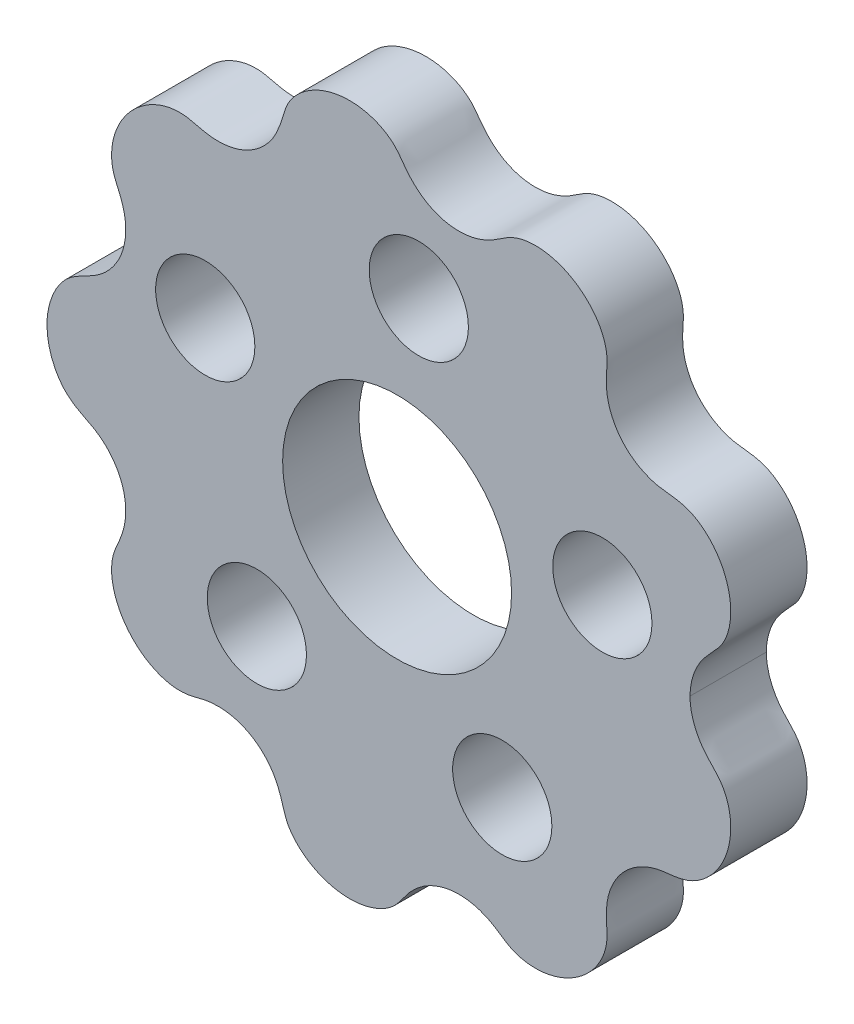
SolidWorks part; units mm, degrees
ref_plane "前视基准面" through (0, 0, 0) normal (0, 0, 1) x (1, 0, 0)
ref_plane "上视基准面" through (0, 0, 0) normal (0, 1, 0) x (1, 0, 0)
ref_plane "右视基准面" through (0, 0, 0) normal (1, 0, 0) x (0, 0, -1)
sketch "草图1" plane through (0, 0, 0) normal (0, 0, 1) x (1, 0, 0)
  line L1 (20.5154, 0) -> (-27.3443, 0) construction
  circle A0 centre (0, 0) radius 6
  spline S0 degree 4 poles (15.4078, 8.5516) (15.5295, 8.4988) (15.7665, 8.3783) (16.0954, 8.1616) (16.4836, 7.8143) (16.8177, 7.4226) (17.0967, 6.997) (17.3205, 6.5428) (17.4876, 6.0676) (17.5964, 5.5785) (17.6455, 5.0823) (17.6342, 4.6444) (17.5834, 4.2711) (17.5188, 3.9944) (17.464, 3.8115) (17.4096, 3.6599) (17.3652, 3.5484) (17.3015, 3.4107) (17.264, 3.3361) (17.1959, 3.2126) (17.1357, 3.1153) (17.0539, 2.995) (16.9466, 2.855) (16.8227, 2.7161) (16.6845, 2.5745) (16.5593, 2.4464) (16.4489, 2.3292) (16.3152, 2.1788) (16.1636, 1.9906) (15.9279, 1.6517) (15.6648, 1.128) (15.5052, 0.5273) (15.4814, -0.1226) (15.5605, -0.6649) (15.6861, -1.0955) (15.8612, -1.486) (16.0723, -1.8343) (16.3083, -2.1405) (16.555, -2.4111) (16.8315, -2.6803) (17.0942, -2.9918) (17.3183, -3.376) (17.4934, -3.8233) (17.6004, -4.2921) (17.6447, -4.77) (17.6284, -5.3454) (17.5114, -6.0091) (17.2782, -6.6442) (16.9371, -7.2268) (16.5751, -7.677) (16.2309, -8.0126) (15.8447, -8.2997) (15.4203, -8.5266) (15.0412, -8.6571) (14.7274, -8.7164) (14.4754, -8.7433) (14.2878, -8.7614) (14.0538, -8.7875) (13.7745, -8.8319) (13.4356, -8.9131) (13.0465, -9.0545) (12.6619, -9.2527) (12.2934, -9.5127) (11.8848, -9.8966) (11.5541, -10.3501) (11.3139, -10.8552) (11.1745, -11.3721) (11.1177, -11.7725) (11.1056, -12.1567) (11.1235, -12.5208) (11.1616, -12.9028) (11.1565, -13.3076) (11.077, -13.7432) (10.9196, -14.1964) (10.6973, -14.6217) (10.4213, -15.0134) (10.0386, -15.4384) (9.5199, -15.8691) (8.9276, -16.2044) (8.283, -16.4293) (7.7098, -16.5364) (7.234, -16.5664) (6.7578, -16.5334) (6.2917, -16.4312) (5.9188, -16.2837) (5.6393, -16.1218) (5.4292, -15.9788) (5.2755, -15.8737) (5.0812, -15.7457) (4.8406, -15.6034) (4.5282, -15.45) (4.1358, -15.3101) (3.7069, -15.2171) (3.2474, -15.184) (2.6836, -15.2243) (2.1404, -15.368) (1.6382, -15.6067) (1.2083, -15.9148) (0.9137, -16.185) (0.6623, -16.4706) (0.4458, -16.7597) (0.2309, -17.073) (-0.0332, -17.3739) (-0.3682, -17.6486) (-0.768, -17.8866) (-1.1977, -18.0655) (-1.6462, -18.1881) (-2.2006, -18.2717) (-2.8603, -18.2759) (-3.5137, -18.1653) (-4.1373, -17.9436) (-4.6414, -17.6775) (-5.0344, -17.4059) (-5.3889, -17.0847) (-5.6928, -16.7155) (-5.9179, -16.3359) (-6.0638, -15.9596) (-6.159, -15.5889) (-6.2647, -15.2412) (-6.4052, -14.8846) (-6.5924, -14.5278) (-6.8329, -14.1799) (-7.1315, -13.853) (-7.5621, -13.4948) (-8.0571, -13.22) (-8.5978, -13.0422) (-9.1415, -12.9705) (-9.5543, -12.969) (-9.8973, -13.0066) (-10.1698, -13.0579) (-10.3944, -13.1114) (-10.5734, -13.1573) (-10.8176, -13.2192) (-11.1325, -13.2755) (-11.5352, -13.2877) (-12.0154, -13.2238) (-12.4807, -13.0889) (-12.9231, -12.8929) (-13.4234, -12.5936) (-13.9487, -12.1614) (-14.3889, -11.6423) (-14.7282, -11.0568) (-14.9397, -10.5253) (-15.0609, -10.069) (-15.1224, -9.6002) (-15.1158, -9.1277) (-15.0429, -8.6926) (-14.9083, -8.3067) (-14.7402, -7.9578) (-14.5979, -7.619) (-14.4775, -7.2504) (-14.3944, -6.8508) (-14.3504, -6.3116) (-14.4076, -5.7493) (-14.5695, -5.2059) (-14.8297, -4.7031) (-15.0937, -4.3326) (-15.3919, -4.0176) (-15.7112, -3.7566) (-16.0007, -3.5689) (-16.2445, -3.4365) (-16.493, -3.3133) (-16.7635, -3.1884) (-17.0822, -3.0075) (-17.4253, -2.7249) (-17.7404, -2.3697) (-18.0007, -1.9724) (-18.2069, -1.5452) (-18.3936, -0.9986) (-18.4981, -0.4259) (-18.5152, 0.1061) (-18.4674, 0.5843) (-18.3989, 0.9586) (-18.2998, 1.3264) (-18.162, 1.6833) (-17.9848, 2.0237) (-17.8279, 2.2658) (-17.712, 2.4219) (-17.6193, 2.534) (-17.5563, 2.6054) (-17.4986, 2.6666) (-17.4495, 2.7166) (-17.3994, 2.7656) (-17.3573, 2.8048) (-17.2912, 2.8633) (-17.2206, 2.9222) (-17.136, 2.9878) (-17.0307, 3.0623) (-16.9018, 3.1436) (-16.7502, 3.2263) (-16.5557, 3.3218) (-16.3265, 3.43) (-16.0686, 3.5654) (-15.7905, 3.7403) (-15.5336, 3.9357) (-15.2572, 4.1901) (-15.0215, 4.4653) (-14.827, 4.7542) (-14.6447, 5.1032) (-14.5035, 5.4638) (-14.396, 5.904) (-14.3548, 6.4206) (-14.386, 6.8105) (-14.4341, 7.0695) (-14.4644, 7.1976) knots 0 0 0 0 0 0.006514 0.013028 0.019259 0.02549 0.031721 0.037951 0.044056 0.05016 0.056265 0.062369 0.065499 0.06863 0.070195 0.07176 0.073325 0.074891 0.076327 0.077763 0.079199 0.080635 0.083508 0.08638 0.088356 0.090332 0.092308 0.094284 0.098235 0.102187 0.112552 0.122904 0.128397 0.133889 0.139373 0.144856 0.149346 0.153836 0.158325 0.162815 0.168293 0.173771 0.180047 0.186323 0.191803 0.197283 0.208243 0.219261 0.22477 0.230279 0.236542 0.242804 0.248311 0.253817 0.25613 0.258442 0.260755 0.263067 0.267692 0.272317 0.277832 0.283347 0.288867 0.294387 0.305265 0.310695 0.316125 0.320597 0.325069 0.329541 0.334013 0.33944 0.344867 0.351176 0.357485 0.362911 0.368338 0.37919 0.390445 0.396072 0.401699 0.407747 0.413796 0.419421 0.425045 0.42733 0.429615 0.431901 0.434186 0.438756 0.443326 0.448958 0.454591 0.46023 0.46587 0.476611 0.481972 0.487332 0.491763 0.496194 0.500625 0.505056 0.510412 0.515769 0.521798 0.527828 0.533186 0.538544 0.549261 0.560079 0.565488 0.570897 0.577186 0.583476 0.588886 0.594295 0.598754 0.603212 0.60767 0.612128 0.61754 0.622952 0.628374 0.633796 0.644955 0.650528 0.656101 0.660637 0.665172 0.667439 0.669707 0.671974 0.674242 0.679808 0.685374 0.691655 0.697935 0.703504 0.709072 0.720208 0.731179 0.736664 0.74215 0.748228 0.754305 0.759791 0.765276 0.769783 0.774291 0.778798 0.783306 0.788793 0.794281 0.805279 0.810848 0.816417 0.821979 0.82754 0.832078 0.836617 0.838886 0.841155 0.845694 0.85125 0.856805 0.862867 0.868928 0.874485 0.880041 0.891155 0.897379 0.900491 0.903603 0.909827 0.916051 0.919226 0.9224 0.923987 0.925574 0.926368 0.927162 0.927955 0.928749 0.929811 0.930873 0.931936 0.932998 0.935122 0.937247 0.939371 0.941496 0.945745 0.9497 0.953655 0.957611 0.961566 0.968116 0.971391 0.974665 0.980874 0.987083 0.993541 1 1 1 1 1 construction
  spline S1 degree 4 poles (15.5, 0) (15.5006, -0.1109) (15.5122, -0.3337) (15.5608, -0.6658) (15.6861, -1.0955) (15.8612, -1.486) (16.0723, -1.8343) (16.3083, -2.1405) (16.555, -2.4111) (16.8315, -2.6803) (17.0942, -2.9918) (17.3183, -3.376) (17.4934, -3.8233) (17.6004, -4.2921) (17.6447, -4.77) (17.6284, -5.3454) (17.5114, -6.0091) (17.2782, -6.6442) (16.9371, -7.2268) (16.5751, -7.677) (16.2309, -8.0126) (15.8447, -8.2997) (15.4203, -8.5266) (15.0412, -8.6571) (14.7274, -8.7164) (14.4754, -8.7433) (14.2878, -8.7614) (14.0538, -8.7875) (13.7745, -8.8319) (13.4356, -8.9131) (13.0465, -9.0545) (12.6619, -9.2527) (12.2934, -9.5127) (11.8848, -9.8966) (11.5541, -10.3501) (11.3139, -10.8552) (11.1745, -11.3721) (11.1177, -11.7725) (11.1056, -12.1567) (11.1235, -12.5208) (11.1616, -12.9028) (11.1565, -13.3076) (11.077, -13.7432) (10.9196, -14.1964) (10.6973, -14.6217) (10.4213, -15.0134) (10.0386, -15.4384) (9.5199, -15.8691) (8.9276, -16.2044) (8.283, -16.4293) (7.7098, -16.5364) (7.234, -16.5664) (6.7578, -16.5334) (6.2917, -16.4312) (5.9188, -16.2837) (5.6393, -16.1218) (5.4292, -15.9788) (5.2755, -15.8737) (5.0812, -15.7457) (4.8406, -15.6034) (4.5282, -15.45) (4.1358, -15.3101) (3.7069, -15.2171) (3.2474, -15.184) (2.6836, -15.2243) (2.1404, -15.368) (1.6382, -15.6067) (1.2083, -15.9148) (0.9137, -16.185) (0.6623, -16.4706) (0.4458, -16.7597) (0.2309, -17.073) (-0.0332, -17.3739) (-0.3682, -17.6486) (-0.768, -17.8866) (-1.1977, -18.0655) (-1.6462, -18.1881) (-2.2006, -18.2717) (-2.8603, -18.2759) (-3.5137, -18.1653) (-4.1373, -17.9436) (-4.6414, -17.6775) (-5.0344, -17.4059) (-5.3889, -17.0847) (-5.6928, -16.7155) (-5.9179, -16.3359) (-6.0638, -15.9596) (-6.159, -15.5889) (-6.2647, -15.2412) (-6.4052, -14.8846) (-6.5924, -14.5278) (-6.8329, -14.1799) (-7.1315, -13.853) (-7.5621, -13.4948) (-8.0571, -13.22) (-8.5978, -13.0422) (-9.1415, -12.9705) (-9.5543, -12.969) (-9.8973, -13.0066) (-10.1698, -13.0579) (-10.3944, -13.1114) (-10.5734, -13.1573) (-10.8176, -13.2192) (-11.1325, -13.2755) (-11.5352, -13.2877) (-12.0154, -13.2238) (-12.4807, -13.0889) (-12.9231, -12.8929) (-13.4234, -12.5936) (-13.9487, -12.1614) (-14.3889, -11.6423) (-14.7282, -11.0568) (-14.9397, -10.5253) (-15.0609, -10.069) (-15.1224, -9.6002) (-15.1158, -9.1277) (-15.0429, -8.6926) (-14.9083, -8.3067) (-14.7402, -7.9578) (-14.5979, -7.619) (-14.4775, -7.2504) (-14.3944, -6.8508) (-14.3504, -6.3116) (-14.4076, -5.7493) (-14.5695, -5.2059) (-14.8297, -4.7031) (-15.0937, -4.3326) (-15.3919, -4.0176) (-15.7112, -3.7566) (-16.0007, -3.5689) (-16.2445, -3.4365) (-16.493, -3.3133) (-16.7635, -3.1884) (-17.0822, -3.0075) (-17.4253, -2.7249) (-17.7404, -2.3697) (-18.0007, -1.9724) (-18.2069, -1.5452) (-18.3924, -1.0021) (-18.4739, -0.5585) (-18.499, -0.2227) (-18.5, 0) knots 0.12295 0.12295 0.12295 0.12295 0.12295 0.128397 0.133889 0.139373 0.144856 0.149346 0.153836 0.158325 0.162815 0.168293 0.173771 0.180047 0.186323 0.191803 0.197283 0.208243 0.219261 0.22477 0.230279 0.236542 0.242804 0.248311 0.253817 0.25613 0.258442 0.260755 0.263067 0.267692 0.272317 0.277832 0.283347 0.288867 0.294387 0.305265 0.310695 0.316125 0.320597 0.325069 0.329541 0.334013 0.33944 0.344867 0.351176 0.357485 0.362911 0.368338 0.37919 0.390445 0.396072 0.401699 0.407747 0.413796 0.419421 0.425045 0.42733 0.429615 0.431901 0.434186 0.438756 0.443326 0.448958 0.454591 0.46023 0.46587 0.476611 0.481972 0.487332 0.491763 0.496194 0.500625 0.505056 0.510412 0.515769 0.521798 0.527828 0.533186 0.538544 0.549261 0.560079 0.565488 0.570897 0.577186 0.583476 0.588886 0.594295 0.598754 0.603212 0.60767 0.612128 0.61754 0.622952 0.628374 0.633796 0.644955 0.650528 0.656101 0.660637 0.665172 0.667439 0.669707 0.671974 0.674242 0.679808 0.685374 0.691655 0.697935 0.703504 0.709072 0.720208 0.731179 0.736664 0.74215 0.748228 0.754305 0.759791 0.765276 0.769783 0.774291 0.778798 0.783306 0.788793 0.794281 0.805279 0.810848 0.816417 0.821979 0.82754 0.832078 0.836617 0.838886 0.841155 0.845694 0.85125 0.856805 0.862867 0.868928 0.874485 0.880041 0.890975 0.890975 0.890975 0.890975 0.890975
  spline S2 degree 4 poles (15.5, 0) (15.5006, 0.1109) (15.5122, 0.3337) (15.5608, 0.6658) (15.6861, 1.0955) (15.8612, 1.486) (16.0723, 1.8343) (16.3083, 2.1405) (16.555, 2.4111) (16.8315, 2.6803) (17.0942, 2.9918) (17.3183, 3.376) (17.4934, 3.8233) (17.6004, 4.2921) (17.6447, 4.77) (17.6284, 5.3454) (17.5114, 6.0091) (17.2782, 6.6442) (16.9371, 7.2268) (16.5751, 7.677) (16.2309, 8.0126) (15.8447, 8.2997) (15.4203, 8.5266) (15.0412, 8.6571) (14.7274, 8.7164) (14.4754, 8.7433) (14.2878, 8.7614) (14.0538, 8.7875) (13.7745, 8.8319) (13.4356, 8.9131) (13.0465, 9.0545) (12.6619, 9.2527) (12.2934, 9.5127) (11.8848, 9.8966) (11.5541, 10.3501) (11.3139, 10.8552) (11.1745, 11.3721) (11.1177, 11.7725) (11.1056, 12.1567) (11.1235, 12.5208) (11.1616, 12.9028) (11.1565, 13.3076) (11.077, 13.7432) (10.9196, 14.1964) (10.6973, 14.6217) (10.4213, 15.0134) (10.0386, 15.4384) (9.5199, 15.8691) (8.9276, 16.2044) (8.283, 16.4293) (7.7098, 16.5364) (7.234, 16.5664) (6.7578, 16.5334) (6.2917, 16.4312) (5.9188, 16.2837) (5.6393, 16.1218) (5.4292, 15.9788) (5.2755, 15.8737) (5.0812, 15.7457) (4.8406, 15.6034) (4.5282, 15.45) (4.1358, 15.3101) (3.7069, 15.2171) (3.2474, 15.184) (2.6836, 15.2243) (2.1404, 15.368) (1.6382, 15.6067) (1.2083, 15.9148) (0.9137, 16.185) (0.6623, 16.4706) (0.4458, 16.7597) (0.2309, 17.073) (-0.0332, 17.3739) (-0.3682, 17.6486) (-0.768, 17.8866) (-1.1977, 18.0655) (-1.6462, 18.1881) (-2.2006, 18.2717) (-2.8603, 18.2759) (-3.5137, 18.1653) (-4.1373, 17.9436) (-4.6414, 17.6775) (-5.0344, 17.4059) (-5.3889, 17.0847) (-5.6928, 16.7155) (-5.9179, 16.3359) (-6.0638, 15.9596) (-6.159, 15.5889) (-6.2647, 15.2412) (-6.4052, 14.8846) (-6.5924, 14.5278) (-6.8329, 14.1799) (-7.1315, 13.853) (-7.5621, 13.4948) (-8.0571, 13.22) (-8.5978, 13.0422) (-9.1415, 12.9705) (-9.5543, 12.969) (-9.8973, 13.0066) (-10.1698, 13.0579) (-10.3944, 13.1114) (-10.5734, 13.1573) (-10.8176, 13.2192) (-11.1325, 13.2755) (-11.5352, 13.2877) (-12.0154, 13.2238) (-12.4807, 13.0889) (-12.9231, 12.8929) (-13.4234, 12.5936) (-13.9487, 12.1614) (-14.3889, 11.6423) (-14.7282, 11.0568) (-14.9397, 10.5253) (-15.0609, 10.069) (-15.1224, 9.6002) (-15.1158, 9.1277) (-15.0429, 8.6926) (-14.9083, 8.3067) (-14.7402, 7.9578) (-14.5979, 7.619) (-14.4775, 7.2504) (-14.3944, 6.8508) (-14.3504, 6.3116) (-14.4076, 5.7493) (-14.5695, 5.2059) (-14.8297, 4.7031) (-15.0937, 4.3326) (-15.3919, 4.0176) (-15.7112, 3.7566) (-16.0007, 3.5689) (-16.2445, 3.4365) (-16.493, 3.3133) (-16.7635, 3.1884) (-17.0822, 3.0075) (-17.4253, 2.7249) (-17.7404, 2.3697) (-18.0007, 1.9724) (-18.2069, 1.5452) (-18.3924, 1.0021) (-18.4739, 0.5585) (-18.499, 0.2227) (-18.5, 0) knots 0.12295 0.12295 0.12295 0.12295 0.12295 0.128397 0.133889 0.139373 0.144856 0.149346 0.153836 0.158325 0.162815 0.168293 0.173771 0.180047 0.186323 0.191803 0.197283 0.208243 0.219261 0.22477 0.230279 0.236542 0.242804 0.248311 0.253817 0.25613 0.258442 0.260755 0.263067 0.267692 0.272317 0.277832 0.283347 0.288867 0.294387 0.305265 0.310695 0.316125 0.320597 0.325069 0.329541 0.334013 0.33944 0.344867 0.351176 0.357485 0.362911 0.368338 0.37919 0.390445 0.396072 0.401699 0.407747 0.413796 0.419421 0.425045 0.42733 0.429615 0.431901 0.434186 0.438756 0.443326 0.448958 0.454591 0.46023 0.46587 0.476611 0.481972 0.487332 0.491763 0.496194 0.500625 0.505056 0.510412 0.515769 0.521798 0.527828 0.533186 0.538544 0.549261 0.560079 0.565488 0.570897 0.577186 0.583476 0.588886 0.594295 0.598754 0.603212 0.60767 0.612128 0.61754 0.622952 0.628374 0.633796 0.644955 0.650528 0.656101 0.660637 0.665172 0.667439 0.669707 0.671974 0.674242 0.679808 0.685374 0.691655 0.697935 0.703504 0.709072 0.720208 0.731179 0.736664 0.74215 0.748228 0.754305 0.759791 0.765276 0.769783 0.774291 0.778798 0.783306 0.788793 0.794281 0.805279 0.810848 0.816417 0.821979 0.82754 0.832078 0.836617 0.838886 0.841155 0.845694 0.85125 0.856805 0.862867 0.868928 0.874485 0.880041 0.890975 0.890975 0.890975 0.890975 0.890975
extrude "凸台-拉伸1" add sketch "草图1" along normal blind 4
sketch "草图2" plane through (0, 0, 4) normal (0, 0, 1) x (1, 0, 0)
  circle A1 centre (5.5114, -9.5197) radius 2.6
  circle A9 centre (-7.3506, -8.1834) radius 2.6
  circle A10 centre (-10.0544, 4.462) radius 2.6
  circle A11 centre (1.1367, 10.9411) radius 2.6
  circle A12 centre (10.7569, 2.2999) radius 2.6
  point P13 (0, 0)
  point P22 (0, 0)
  dimension "D1" = 5
extrude "切除-拉伸1" cut sketch "草图2" against normal blind 4
sketch "草图3" plane through (0, 0, 4) normal (0, 0, 1) x (1, 0, 0)
  spline S0 degree 4 poles (1623.4562, 1732.6571) (562.2442, -2347.7402) (172.4823, 104.3908) (-26.5264, 22.8102) (-18.2069, -1.5452) (-18.0007, -1.9724) (-17.7404, -2.3697) (-17.4253, -2.7249) (-17.0822, -3.0075) (-16.7635, -3.1884) (-16.493, -3.3133) (-16.2445, -3.4365) (-16.0007, -3.5689) (-15.7112, -3.7566) (-15.3919, -4.0176) (-15.0937, -4.3326) (-14.8297, -4.7031) (-14.5695, -5.2059) (-14.4076, -5.7493) (-14.3504, -6.3116) (-14.3944, -6.8508) (-14.4775, -7.2504) (-14.5979, -7.619) (-14.7402, -7.9578) (-14.9083, -8.3067) (-15.0429, -8.6926) (-15.1158, -9.1277) (-15.1224, -9.6002) (-15.0609, -10.069) (-14.9397, -10.5253) (-14.7282, -11.0568) (-14.3889, -11.6423) (-13.9487, -12.1614) (-13.4234, -12.5936) (-12.9231, -12.8929) (-12.4807, -13.0889) (-12.0154, -13.2238) (-11.5352, -13.2877) (-11.1325, -13.2755) (-10.8176, -13.2192) (-10.5734, -13.1573) (-10.3944, -13.1114) (-10.1698, -13.0579) (-9.8973, -13.0066) (-9.5543, -12.969) (-9.1415, -12.9705) (-8.5978, -13.0422) (-8.0571, -13.22) (-7.5621, -13.4948) (-7.1315, -13.853) (-6.8329, -14.1799) (-6.5924, -14.5278) (-6.4052, -14.8846) (-6.2647, -15.2412) (-6.159, -15.5889) (-6.0638, -15.9596) (-5.9179, -16.3359) (-5.6928, -16.7155) (-5.3889, -17.0847) (-5.0344, -17.4059) (-4.6414, -17.6775) (-4.1373, -17.9436) (-3.5137, -18.1653) (-2.8603, -18.2759) (-2.2006, -18.2717) (-1.6462, -18.1881) (-1.1977, -18.0655) (-0.768, -17.8866) (-0.3682, -17.6486) (-0.0332, -17.3739) (0.2309, -17.073) (0.4458, -16.7597) (0.6623, -16.4706) (0.9137, -16.185) (1.2083, -15.9148) (1.6382, -15.6067) (2.1404, -15.368) (2.6836, -15.2243) (3.2474, -15.184) (3.7069, -15.2171) (4.1358, -15.3101) (4.5282, -15.45) (4.8406, -15.6034) (5.0812, -15.7457) (5.2755, -15.8737) (5.4292, -15.9788) (5.6393, -16.1218) (5.9188, -16.2837) (6.2917, -16.4312) (6.7578, -16.5334) (7.234, -16.5664) (7.7098, -16.5364) (8.283, -16.4293) (8.9276, -16.2044) (9.5199, -15.8691) (10.0386, -15.4384) (10.4213, -15.0134) (10.6973, -14.6217) (10.9196, -14.1964) (11.077, -13.7432) (11.1565, -13.3076) (11.1616, -12.9028) (11.1235, -12.5208) (11.1056, -12.1567) (11.1177, -11.7725) (11.1745, -11.3721) (11.3139, -10.8552) (11.5541, -10.3501) (11.8848, -9.8966) (12.2934, -9.5127) (12.6619, -9.2527) (13.0465, -9.0545) (13.4356, -8.9131) (13.7745, -8.8319) (14.0538, -8.7875) (14.2878, -8.7614) (14.4754, -8.7433) (14.7274, -8.7164) (15.0412, -8.6571) (15.4203, -8.5266) (15.8447, -8.2997) (16.2309, -8.0126) (16.5751, -7.677) (16.9371, -7.2268) (17.2782, -6.6442) (17.5114, -6.0091) (17.6284, -5.3454) (17.6447, -4.77) (17.6004, -4.2921) (17.4934, -3.8233) (17.3183, -3.376) (17.0942, -2.9918) (16.8315, -2.6803) (16.555, -2.4111) (16.3083, -2.1405) (16.0723, -1.8343) (15.8612, -1.486) (15.6861, -1.0955) (13.1065, 7.7509) (43.9529, 23.7285) (146.1118, -134.5096) (-2647.3681, -1370.9416) knots -1.109563 -1.109563 -1.109563 -1.109563 -1.109563 0.133883 0.139439 0.144996 0.151057 0.157119 0.162675 0.16823 0.172769 0.175038 0.177307 0.181846 0.186384 0.191946 0.197507 0.203076 0.208646 0.219643 0.225131 0.230618 0.235126 0.239633 0.244141 0.248648 0.254134 0.259619 0.265697 0.271774 0.27726 0.282745 0.293717 0.304853 0.310421 0.315989 0.32227 0.32855 0.334116 0.339682 0.34195 0.344217 0.346485 0.348753 0.353288 0.357823 0.363396 0.368969 0.380129 0.385551 0.390973 0.396384 0.401796 0.406254 0.410712 0.415171 0.419629 0.425038 0.430448 0.436738 0.443027 0.448436 0.453845 0.464663 0.47538 0.480738 0.486096 0.492126 0.498156 0.503512 0.508869 0.513299 0.51773 0.522161 0.526592 0.531952 0.537313 0.548055 0.553694 0.559334 0.564966 0.570598 0.575168 0.579739 0.582024 0.584309 0.586594 0.588879 0.594504 0.600128 0.606177 0.612225 0.617852 0.62348 0.634734 0.645587 0.651013 0.656439 0.662748 0.669057 0.674484 0.679912 0.684383 0.688855 0.693327 0.697799 0.703229 0.708659 0.719537 0.725057 0.730577 0.736092 0.741607 0.746232 0.750857 0.753169 0.755482 0.757794 0.760107 0.765614 0.77112 0.777383 0.783645 0.789154 0.794663 0.805681 0.816641 0.822121 0.827601 0.833877 0.840153 0.845631 0.85111 0.855599 0.860089 0.864578 0.869068 0.874551 0.880035 0.885528 1.319982 1.319982 1.319982 1.319982 1.319982 only from (-18.5, 0) to (15.5, 0) construction
  spline S1 degree 4 poles (-18.5, 0) (-18.499, -0.2227) (-18.4739, -0.5585) (-18.3924, -1.0021) (-18.2069, -1.5452) (-18.0007, -1.9724) (-17.7404, -2.3697) (-17.4253, -2.7249) (-17.0822, -3.0075) (-16.7635, -3.1884) (-16.493, -3.3133) (-16.2445, -3.4365) (-16.0007, -3.5689) (-15.7112, -3.7566) (-15.3919, -4.0176) (-15.0937, -4.3326) (-14.8297, -4.7031) (-14.5695, -5.2059) (-14.4076, -5.7493) (-14.3504, -6.3116) (-14.3944, -6.8508) (-14.4775, -7.2504) (-14.5979, -7.619) (-14.7402, -7.9578) (-14.9083, -8.3067) (-15.0429, -8.6926) (-15.1158, -9.1277) (-15.1224, -9.6002) (-15.0609, -10.069) (-14.9397, -10.5253) (-14.7282, -11.0568) (-14.3889, -11.6423) (-13.9487, -12.1614) (-13.4234, -12.5936) (-12.9231, -12.8929) (-12.4807, -13.0889) (-12.0154, -13.2238) (-11.5352, -13.2877) (-11.1325, -13.2755) (-10.8176, -13.2192) (-10.5734, -13.1573) (-10.3944, -13.1114) (-10.1698, -13.0579) (-9.8973, -13.0066) (-9.5543, -12.969) (-9.1415, -12.9705) (-8.5978, -13.0422) (-8.0571, -13.22) (-7.5621, -13.4948) (-7.1315, -13.853) (-6.8329, -14.1799) (-6.5924, -14.5278) (-6.4052, -14.8846) (-6.2647, -15.2412) (-6.159, -15.5889) (-6.0638, -15.9596) (-5.9179, -16.3359) (-5.6928, -16.7155) (-5.3889, -17.0847) (-5.0344, -17.4059) (-4.6414, -17.6775) (-4.1373, -17.9436) (-3.5137, -18.1653) (-2.8603, -18.2759) (-2.2006, -18.2717) (-1.6462, -18.1881) (-1.1977, -18.0655) (-0.768, -17.8866) (-0.3682, -17.6486) (-0.0332, -17.3739) (0.2309, -17.073) (0.4458, -16.7597) (0.6623, -16.4706) (0.9137, -16.185) (1.2083, -15.9148) (1.6382, -15.6067) (2.1404, -15.368) (2.6836, -15.2243) (3.2474, -15.184) (3.7069, -15.2171) (4.1358, -15.3101) (4.5282, -15.45) (4.8406, -15.6034) (5.0812, -15.7457) (5.2755, -15.8737) (5.4292, -15.9788) (5.6393, -16.1218) (5.9188, -16.2837) (6.2917, -16.4312) (6.7578, -16.5334) (7.234, -16.5664) (7.7098, -16.5364) (8.283, -16.4293) (8.9276, -16.2044) (9.5199, -15.8691) (10.0386, -15.4384) (10.4213, -15.0134) (10.6973, -14.6217) (10.9196, -14.1964) (11.077, -13.7432) (11.1565, -13.3076) (11.1616, -12.9028) (11.1235, -12.5208) (11.1056, -12.1567) (11.1177, -11.7725) (11.1745, -11.3721) (11.3139, -10.8552) (11.5541, -10.3501) (11.8848, -9.8966) (12.2934, -9.5127) (12.6619, -9.2527) (13.0465, -9.0545) (13.4356, -8.9131) (13.7745, -8.8319) (14.0538, -8.7875) (14.2878, -8.7614) (14.4754, -8.7433) (14.7274, -8.7164) (15.0412, -8.6571) (15.4203, -8.5266) (15.8447, -8.2997) (16.2309, -8.0126) (16.5751, -7.677) (16.9371, -7.2268) (17.2782, -6.6442) (17.5114, -6.0091) (17.6284, -5.3454) (17.6447, -4.77) (17.6004, -4.2921) (17.4934, -3.8233) (17.3183, -3.376) (17.0942, -2.9918) (16.8315, -2.6803) (16.555, -2.4111) (16.3083, -2.1405) (16.0723, -1.8343) (15.8612, -1.486) (15.6861, -1.0955) (15.5608, -0.6658) (15.5122, -0.3337) (15.5006, -0.1109) (15.5, 0) knots 0.12295 0.12295 0.12295 0.12295 0.12295 0.133883 0.139439 0.144996 0.151057 0.157119 0.162675 0.16823 0.172769 0.175038 0.177307 0.181846 0.186384 0.191946 0.197507 0.203076 0.208646 0.219643 0.225131 0.230618 0.235126 0.239633 0.244141 0.248648 0.254134 0.259619 0.265697 0.271774 0.27726 0.282745 0.293717 0.304853 0.310421 0.315989 0.32227 0.32855 0.334116 0.339682 0.34195 0.344217 0.346485 0.348753 0.353288 0.357823 0.363396 0.368969 0.380129 0.385551 0.390973 0.396384 0.401796 0.406254 0.410712 0.415171 0.419629 0.425038 0.430448 0.436738 0.443027 0.448436 0.453845 0.464663 0.47538 0.480738 0.486096 0.492126 0.498156 0.503512 0.508869 0.513299 0.51773 0.522161 0.526592 0.531952 0.537313 0.548055 0.553694 0.559334 0.564966 0.570598 0.575168 0.579739 0.582024 0.584309 0.586594 0.588879 0.594504 0.600128 0.606177 0.612225 0.617852 0.62348 0.634734 0.645587 0.651013 0.656439 0.662748 0.669057 0.674484 0.679912 0.684383 0.688855 0.693327 0.697799 0.703229 0.708659 0.719537 0.725057 0.730577 0.736092 0.741607 0.746232 0.750857 0.753169 0.755482 0.757794 0.760107 0.765614 0.77112 0.777383 0.783645 0.789154 0.794663 0.805681 0.816641 0.822121 0.827601 0.833877 0.840153 0.845631 0.85111 0.855599 0.860089 0.864578 0.869068 0.874551 0.880035 0.885528 0.890975 0.890975 0.890975 0.890975 0.890975
  spline S2 degree 4 poles (-2647.7561, 1371.1133) (146.1223, 134.5259) (43.955, -23.7296) (13.1064, -7.7512) (15.6861, 1.0955) (15.8612, 1.486) (16.0723, 1.8343) (16.3083, 2.1405) (16.555, 2.4111) (16.8315, 2.6803) (17.0942, 2.9918) (17.3183, 3.376) (17.4934, 3.8233) (17.6004, 4.2921) (17.6447, 4.77) (17.6284, 5.3454) (17.5114, 6.0091) (17.2782, 6.6442) (16.9371, 7.2268) (16.5751, 7.677) (16.2309, 8.0126) (15.8447, 8.2997) (15.4203, 8.5266) (15.0412, 8.6571) (14.7274, 8.7164) (14.4754, 8.7433) (14.2878, 8.7614) (14.0538, 8.7875) (13.7745, 8.8319) (13.4356, 8.9131) (13.0465, 9.0545) (12.6619, 9.2527) (12.2934, 9.5127) (11.8848, 9.8966) (11.5541, 10.3501) (11.3139, 10.8552) (11.1745, 11.3721) (11.1177, 11.7725) (11.1056, 12.1567) (11.1235, 12.5208) (11.1616, 12.9028) (11.1565, 13.3076) (11.077, 13.7432) (10.9196, 14.1964) (10.6973, 14.6217) (10.4213, 15.0134) (10.0386, 15.4384) (9.5199, 15.8691) (8.9276, 16.2044) (8.283, 16.4293) (7.7098, 16.5364) (7.234, 16.5664) (6.7578, 16.5334) (6.2917, 16.4312) (5.9188, 16.2837) (5.6393, 16.1218) (5.4292, 15.9788) (5.2755, 15.8737) (5.0812, 15.7457) (4.8406, 15.6034) (4.5282, 15.45) (4.1358, 15.3101) (3.7069, 15.2171) (3.2474, 15.184) (2.6836, 15.2243) (2.1404, 15.368) (1.6382, 15.6067) (1.2083, 15.9148) (0.9137, 16.185) (0.6623, 16.4706) (0.4458, 16.7597) (0.2309, 17.073) (-0.0332, 17.3739) (-0.3682, 17.6486) (-0.768, 17.8866) (-1.1977, 18.0655) (-1.6462, 18.1881) (-2.2006, 18.2717) (-2.8603, 18.2759) (-3.5137, 18.1653) (-4.1373, 17.9436) (-4.6414, 17.6775) (-5.0344, 17.4059) (-5.3889, 17.0847) (-5.6928, 16.7155) (-5.9179, 16.3359) (-6.0638, 15.9596) (-6.159, 15.5889) (-6.2647, 15.2412) (-6.4052, 14.8846) (-6.5924, 14.5278) (-6.8329, 14.1799) (-7.1315, 13.853) (-7.5621, 13.4948) (-8.0571, 13.22) (-8.5978, 13.0422) (-9.1415, 12.9705) (-9.5543, 12.969) (-9.8973, 13.0066) (-10.1698, 13.0579) (-10.3944, 13.1114) (-10.5734, 13.1573) (-10.8176, 13.2192) (-11.1325, 13.2755) (-11.5352, 13.2877) (-12.0154, 13.2238) (-12.4807, 13.0889) (-12.9231, 12.8929) (-13.4234, 12.5936) (-13.9487, 12.1614) (-14.3889, 11.6423) (-14.7282, 11.0568) (-14.9397, 10.5253) (-15.0609, 10.069) (-15.1224, 9.6002) (-15.1158, 9.1277) (-15.0429, 8.6926) (-14.9083, 8.3067) (-14.7402, 7.9578) (-14.5979, 7.619) (-14.4775, 7.2504) (-14.3944, 6.8508) (-14.3504, 6.3116) (-14.4076, 5.7493) (-14.5695, 5.2059) (-14.8297, 4.7031) (-15.0937, 4.3326) (-15.3919, 4.0176) (-15.7112, 3.7566) (-16.0007, 3.5689) (-16.2445, 3.4365) (-16.493, 3.3133) (-16.7635, 3.1884) (-17.0822, 3.0075) (-17.4253, 2.7249) (-17.7404, 2.3697) (-18.0007, 1.9724) (-18.2069, 1.5452) (-26.5265, -22.8105) (172.4881, -104.3932) (562.2612, 2347.8471) (1623.5182, -1732.8954) knots -0.306073 -0.306073 -0.306073 -0.306073 -0.306073 0.128397 0.133889 0.139373 0.144856 0.149346 0.153836 0.158325 0.162815 0.168293 0.173771 0.180047 0.186323 0.191803 0.197283 0.208243 0.219261 0.22477 0.230279 0.236542 0.242804 0.248311 0.253817 0.25613 0.258442 0.260755 0.263067 0.267692 0.272317 0.277832 0.283347 0.288867 0.294387 0.305265 0.310695 0.316125 0.320597 0.325069 0.329541 0.334013 0.33944 0.344867 0.351176 0.357485 0.362911 0.368338 0.37919 0.390445 0.396072 0.401699 0.407747 0.413796 0.419421 0.425045 0.42733 0.429615 0.431901 0.434186 0.438756 0.443326 0.448958 0.454591 0.46023 0.46587 0.476611 0.481972 0.487332 0.491763 0.496194 0.500625 0.505056 0.510412 0.515769 0.521798 0.527828 0.533186 0.538544 0.549261 0.560079 0.565488 0.570897 0.577186 0.583476 0.588886 0.594295 0.598754 0.603212 0.60767 0.612128 0.61754 0.622952 0.628374 0.633796 0.644955 0.650528 0.656101 0.660637 0.665172 0.667439 0.669707 0.671974 0.674242 0.679808 0.685374 0.691655 0.697935 0.703504 0.709072 0.720208 0.731179 0.736664 0.74215 0.748228 0.754305 0.759791 0.765276 0.769783 0.774291 0.778798 0.783306 0.788793 0.794281 0.805279 0.810848 0.816417 0.821979 0.82754 0.832078 0.836617 0.838886 0.841155 0.845694 0.85125 0.856805 0.862867 0.868928 0.874485 0.880041 2.123506 2.123506 2.123506 2.123506 2.123506 only from (15.5, 0) to (-18.5, 0) construction
  spline S3 degree 4 poles (15.5, 0) (15.5006, 0.1109) (15.5122, 0.3337) (15.5608, 0.6658) (15.6861, 1.0955) (15.8612, 1.486) (16.0723, 1.8343) (16.3083, 2.1405) (16.555, 2.4111) (16.8315, 2.6803) (17.0942, 2.9918) (17.3183, 3.376) (17.4934, 3.8233) (17.6004, 4.2921) (17.6447, 4.77) (17.6284, 5.3454) (17.5114, 6.0091) (17.2782, 6.6442) (16.9371, 7.2268) (16.5751, 7.677) (16.2309, 8.0126) (15.8447, 8.2997) (15.4203, 8.5266) (15.0412, 8.6571) (14.7274, 8.7164) (14.4754, 8.7433) (14.2878, 8.7614) (14.0538, 8.7875) (13.7745, 8.8319) (13.4356, 8.9131) (13.0465, 9.0545) (12.6619, 9.2527) (12.2934, 9.5127) (11.8848, 9.8966) (11.5541, 10.3501) (11.3139, 10.8552) (11.1745, 11.3721) (11.1177, 11.7725) (11.1056, 12.1567) (11.1235, 12.5208) (11.1616, 12.9028) (11.1565, 13.3076) (11.077, 13.7432) (10.9196, 14.1964) (10.6973, 14.6217) (10.4213, 15.0134) (10.0386, 15.4384) (9.5199, 15.8691) (8.9276, 16.2044) (8.283, 16.4293) (7.7098, 16.5364) (7.234, 16.5664) (6.7578, 16.5334) (6.2917, 16.4312) (5.9188, 16.2837) (5.6393, 16.1218) (5.4292, 15.9788) (5.2755, 15.8737) (5.0812, 15.7457) (4.8406, 15.6034) (4.5282, 15.45) (4.1358, 15.3101) (3.7069, 15.2171) (3.2474, 15.184) (2.6836, 15.2243) (2.1404, 15.368) (1.6382, 15.6067) (1.2083, 15.9148) (0.9137, 16.185) (0.6623, 16.4706) (0.4458, 16.7597) (0.2309, 17.073) (-0.0332, 17.3739) (-0.3682, 17.6486) (-0.768, 17.8866) (-1.1977, 18.0655) (-1.6462, 18.1881) (-2.2006, 18.2717) (-2.8603, 18.2759) (-3.5137, 18.1653) (-4.1373, 17.9436) (-4.6414, 17.6775) (-5.0344, 17.4059) (-5.3889, 17.0847) (-5.6928, 16.7155) (-5.9179, 16.3359) (-6.0638, 15.9596) (-6.159, 15.5889) (-6.2647, 15.2412) (-6.4052, 14.8846) (-6.5924, 14.5278) (-6.8329, 14.1799) (-7.1315, 13.853) (-7.5621, 13.4948) (-8.0571, 13.22) (-8.5978, 13.0422) (-9.1415, 12.9705) (-9.5543, 12.969) (-9.8973, 13.0066) (-10.1698, 13.0579) (-10.3944, 13.1114) (-10.5734, 13.1573) (-10.8176, 13.2192) (-11.1325, 13.2755) (-11.5352, 13.2877) (-12.0154, 13.2238) (-12.4807, 13.0889) (-12.9231, 12.8929) (-13.4234, 12.5936) (-13.9487, 12.1614) (-14.3889, 11.6423) (-14.7282, 11.0568) (-14.9397, 10.5253) (-15.0609, 10.069) (-15.1224, 9.6002) (-15.1158, 9.1277) (-15.0429, 8.6926) (-14.9083, 8.3067) (-14.7402, 7.9578) (-14.5979, 7.619) (-14.4775, 7.2504) (-14.3944, 6.8508) (-14.3504, 6.3116) (-14.4076, 5.7493) (-14.5695, 5.2059) (-14.8297, 4.7031) (-15.0937, 4.3326) (-15.3919, 4.0176) (-15.7112, 3.7566) (-16.0007, 3.5689) (-16.2445, 3.4365) (-16.493, 3.3133) (-16.7635, 3.1884) (-17.0822, 3.0075) (-17.4253, 2.7249) (-17.7404, 2.3697) (-18.0007, 1.9724) (-18.2069, 1.5452) (-18.3924, 1.0021) (-18.4739, 0.5585) (-18.499, 0.2227) (-18.5, 0) knots 0.12295 0.12295 0.12295 0.12295 0.12295 0.128397 0.133889 0.139373 0.144856 0.149346 0.153836 0.158325 0.162815 0.168293 0.173771 0.180047 0.186323 0.191803 0.197283 0.208243 0.219261 0.22477 0.230279 0.236542 0.242804 0.248311 0.253817 0.25613 0.258442 0.260755 0.263067 0.267692 0.272317 0.277832 0.283347 0.288867 0.294387 0.305265 0.310695 0.316125 0.320597 0.325069 0.329541 0.334013 0.33944 0.344867 0.351176 0.357485 0.362911 0.368338 0.37919 0.390445 0.396072 0.401699 0.407747 0.413796 0.419421 0.425045 0.42733 0.429615 0.431901 0.434186 0.438756 0.443326 0.448958 0.454591 0.46023 0.46587 0.476611 0.481972 0.487332 0.491763 0.496194 0.500625 0.505056 0.510412 0.515769 0.521798 0.527828 0.533186 0.538544 0.549261 0.560079 0.565488 0.570897 0.577186 0.583476 0.588886 0.594295 0.598754 0.603212 0.60767 0.612128 0.61754 0.622952 0.628374 0.633796 0.644955 0.650528 0.656101 0.660637 0.665172 0.667439 0.669707 0.671974 0.674242 0.679808 0.685374 0.691655 0.697935 0.703504 0.709072 0.720208 0.731179 0.736664 0.74215 0.748228 0.754305 0.759791 0.765276 0.769783 0.774291 0.778798 0.783306 0.788793 0.794281 0.805279 0.810848 0.816417 0.821979 0.82754 0.832078 0.836617 0.838886 0.841155 0.845694 0.85125 0.856805 0.862867 0.868928 0.874485 0.880041 0.890975 0.890975 0.890975 0.890975 0.890975
  spline S4 degree 1 poles (-18.35, 0) (15.35, 0) knots 0 0 1 1 construction
  spline S5 degree 1 poles (15.35, 0) (-18.35, 0) knots 0 0 1 1 construction
  spline S6 degree 3 poles (-18.35, 0) (-18.3472, -0.6215) (-18.1231, -1.5691) (-17.3904, -2.6083) (-16.6299, -3.1102) (-15.6965, -3.5255) (-14.9367, -4.2302) (-14.4096, -5.1199) (-14.1804, -6.1305) (-14.2562, -7.1606) (-14.5767, -7.9605) (-14.8395, -8.5327) (-14.9815, -9.1309) (-14.9653, -9.919) (-14.6926, -10.8259) (-14.2104, -11.6434) (-13.5526, -12.3285) (-12.7558, -12.8397) (-11.8513, -13.1363) (-10.932, -13.1356) (-9.9848, -12.8228) (-8.9471, -12.7998) (-7.9508, -13.0743) (-7.0829, -13.6408) (-6.4227, -14.436) (-6.0363, -15.398) (-5.8169, -16.3209) (-5.2357, -17.0643) (-4.479, -17.6314) (-3.31, -18.116) (-2.0185, -18.1795) (-0.8207, -17.7778) (-0.0486, -17.249) (0.4644, -16.4309) (1.1883, -15.6875) (2.0972, -15.1959) (3.1147, -14.9976) (4.1412, -15.1154) (5.0932, -15.5294) (5.8621, -16.1401) (6.749, -16.4118) (7.6984, -16.4149) (8.9228, -16.1025) (9.9922, -15.3743) (10.7165, -14.3408) (10.9763, -13.5965) (11.018, -12.9853) (10.9538, -12.3457) (10.961, -11.1396) (11.5909, -9.8584) (12.6878, -9.0222) (13.6572, -8.6539) (14.6672, -8.6086) (15.5412, -8.3449) (16.3076, -7.7768) (17.1002, -6.796) (17.5159, -5.5702) (17.4797, -4.3074) (17.2499, -3.5539) (16.9334, -3.0238) (16.5123, -2.5688) (15.6784, -1.7061) (15.3538, -0.6714) (15.35, 0) knots 0.122958 0.122958 0.122958 0.122958 0.146959 0.158959 0.17096 0.18296 0.19496 0.206961 0.218961 0.230962 0.242962 0.248962 0.254963 0.266963 0.278963 0.290964 0.302964 0.314965 0.326965 0.338966 0.350966 0.362966 0.374967 0.386967 0.398968 0.410968 0.422969 0.434969 0.446969 0.45897 0.482971 0.494971 0.506971 0.518972 0.530972 0.542973 0.554973 0.566974 0.578974 0.590974 0.602975 0.614975 0.626976 0.650977 0.662977 0.674977 0.680978 0.686978 0.698978 0.722979 0.73498 0.74698 0.75898 0.770981 0.782981 0.794982 0.818983 0.830983 0.842983 0.848984 0.854984 0.866984 0.890985 0.890985 0.890985 0.890985
  spline S7 degree 3 poles (15.35, 0) (15.3538, 0.6714) (15.6784, 1.7061) (16.5123, 2.5688) (16.9334, 3.0238) (17.2499, 3.5539) (17.4797, 4.3074) (17.5159, 5.5702) (17.1002, 6.796) (16.3076, 7.7768) (15.5412, 8.3449) (14.6672, 8.6086) (13.6572, 8.6539) (12.6878, 9.0222) (11.5909, 9.8584) (10.961, 11.1396) (10.9538, 12.3457) (11.018, 12.9853) (10.9763, 13.5965) (10.7165, 14.3408) (9.9922, 15.3743) (8.9228, 16.1025) (7.6984, 16.4149) (6.749, 16.4118) (5.8621, 16.1401) (5.0932, 15.5294) (4.1412, 15.1154) (3.1147, 14.9976) (2.0972, 15.1959) (1.1883, 15.6875) (0.4644, 16.4309) (-0.0486, 17.249) (-0.8207, 17.7778) (-2.0185, 18.1795) (-3.31, 18.116) (-4.479, 17.6314) (-5.2357, 17.0643) (-5.8169, 16.3209) (-6.0363, 15.398) (-6.4227, 14.436) (-7.0829, 13.6408) (-7.9508, 13.0743) (-8.9471, 12.7998) (-9.9848, 12.8228) (-10.932, 13.1356) (-11.8513, 13.1363) (-12.7558, 12.8397) (-13.5526, 12.3285) (-14.2104, 11.6434) (-14.6926, 10.8259) (-14.9653, 9.919) (-14.9815, 9.1309) (-14.8395, 8.5327) (-14.5767, 7.9605) (-14.2562, 7.1606) (-14.1804, 6.1305) (-14.4096, 5.1199) (-14.9367, 4.2302) (-15.6965, 3.5255) (-16.6299, 3.1102) (-17.3904, 2.6083) (-18.1231, 1.5691) (-18.3472, 0.6215) (-18.35, 0) knots 0.122939 0.122939 0.122939 0.122939 0.14694 0.15894 0.164941 0.170941 0.182941 0.194942 0.218943 0.230943 0.242943 0.254944 0.266944 0.278945 0.290945 0.314946 0.326946 0.332947 0.338947 0.350947 0.362948 0.386948 0.398949 0.410949 0.42295 0.43495 0.446951 0.458951 0.470951 0.482952 0.494952 0.506953 0.518953 0.530954 0.554954 0.566955 0.578955 0.590956 0.602956 0.614957 0.626957 0.638957 0.650958 0.662958 0.674959 0.686959 0.69896 0.71096 0.72296 0.734961 0.746961 0.758962 0.764962 0.770962 0.782962 0.794963 0.806963 0.818964 0.830964 0.842965 0.854965 0.866965 0.890966 0.890966 0.890966 0.890966
  dimension "D1" = 0.15
extrude "切除-拉伸2" cut sketch "草图3" against normal blind 20
